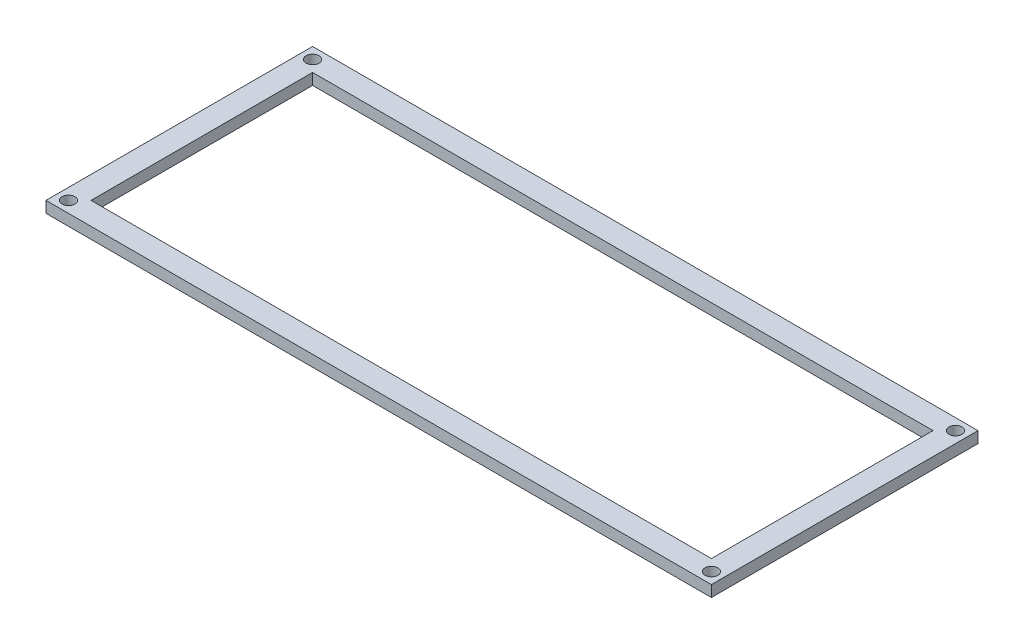
SolidWorks part; units mm, degrees
material "6061-T6 (SS)"
ref_plane "Front Plane" through (0, 0, 0) normal (0, 0, 1) x (1, 0, 0)
ref_plane "Top Plane" through (0, 0, 0) normal (0, 1, 0) x (1, 0, 0)
ref_plane "Right Plane" through (0, 0, 0) normal (1, 0, 0) x (0, 0, -1)
sketch "Sketch1" plane through (0, 0, 0) normal (0, 1, 0) x (1, 0, 0)
  line L0 (-75.08, 30.08) -> (75.08, 30.08)
  line L1 (-70, -25) -> (70, -25)
  line L2 (-70, -25) -> (-70, 25)
  line L3 (-70, 25) -> (70, 25)
  line L4 (70, -25) -> (70, 25)
  line L5 (-70, -25) -> (70, 25) construction
  line L6 (-70, 25) -> (70, -25) construction
  line L7 (75.08, -30.08) -> (75.08, 30.08)
  line L8 (-75.08, -30.08) -> (75.08, -30.08)
  line L9 (-75.08, -30.08) -> (-75.08, 30.08)
  point P0 (0, 0)
  dimension "D2" = 140
  dimension "D3" = 50
  dimension "D1" = 5.08
extrude "Boss-Extrude1" add sketch "Sketch1" along normal blind 2.54 contours L9 L0 L7 L8
sketch "Sketch2" plane through (0, 2.54, 0) normal (0, 1, 0) x (1, 0, 0)
  line L0 (70, -25) -> (75.08, -30.08) construction
  line L1 (70, 0) -> (-70, 0) construction
  line L2 (70, -25) -> (70, 25) construction
  line L3 (-70, 25) -> (-70, -25) construction
  line L4 (0, -25) -> (0, 25) construction
  line L5 (-70, -25) -> (70, -25) construction
  line L6 (70, 25) -> (-70, 25) construction
  circle A0 centre (72.54, -27.54) radius 1.4605
  circle A1 centre (72.54, 27.54) radius 1.4605
  circle A2 centre (-72.54, 27.54) radius 1.4605
  circle A3 centre (-72.54, -27.54) radius 1.4605
  dimension "D1" = 2.921
extrude "Mounting Holes (4-40 Clearance)" cut sketch "Sketch2" against normal blind 2.54
equation "\"Length Needed for Telemetry\"= 140mm"
equation "\"D2@Sketch1\"=\"Length Needed for Telemetry\""
equation "\"Width Needed for Telemetry\" = 50mm"
equation "\"D3@Sketch1\"=\"Width Needed for Telemetry\""
